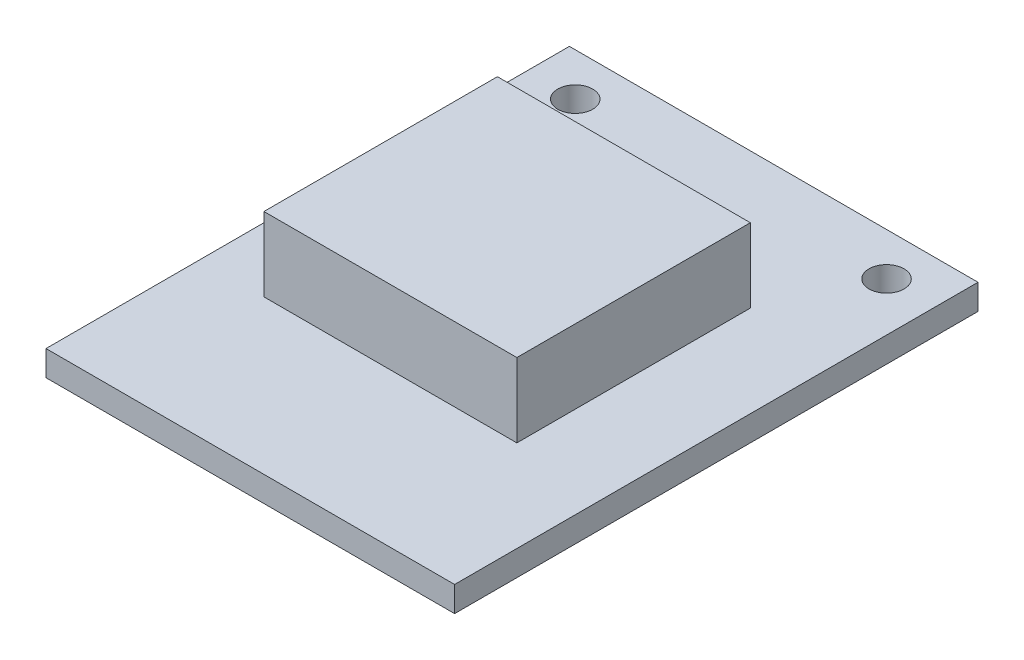
SolidWorks part; units mm, degrees
ref_plane "Front Plane" through (0, 0, 0) normal (0, 0, 1) x (1, 0, 0)
ref_plane "Top Plane" through (0, 0, 0) normal (0, 1, 0) x (1, 0, 0)
ref_plane "Right Plane" through (0, 0, 0) normal (1, 0, 0) x (0, 0, -1)
sketch "Sketch1" plane through (0, 0, 0) normal (0, 1, 0) x (1, 0, 0)
  line L0 (1.143, 0) -> (19.177, 0) construction
  line L1 (10.16, 2.794) -> (10.16, 0) construction
  line L3 (-3.175, 2.794) -> (23.495, 2.794)
  line L4 (-3.175, 2.794) -> (-3.175, -31.369)
  line L5 (-3.175, -31.369) -> (23.495, -31.369)
  line L6 (23.495, 2.794) -> (23.495, -31.369)
  circle A0 centre (0, 0) radius 1.143
  circle A1 centre (20.32, 0) radius 1.143
  point P5 (1.143, 0)
  point P6 (19.177, 0)
  point P7 (-1.143, 0)
  point P14 (21.463, 0)
  point P15 (0, 1.143)
  dimension "D1" = 18.034
  dimension "D2" = 22.606
  dimension "D3" = 26.67
  dimension "D4" = 34.163
  dimension "D5" = 1.651
extrude "Boss-Extrude1" add sketch "Sketch1" along normal blind 1.651
sketch "Sketch2" plane through (0, 1.651, 0) normal (0, 1, 0) x (1, 0, 0)
  line L1 (1.016, -6.096) -> (17.526, -6.096)
  line L2 (1.016, -6.096) -> (1.016, -21.336)
  line L3 (1.016, -21.336) -> (17.526, -21.336)
  line L4 (17.526, -6.096) -> (17.526, -21.336)
  line L8 (-3.175, 2.794) -> (-3.175, -31.369)
  line L9 (-3.175, -31.369) -> (23.495, -31.369)
  line L10 (23.495, -31.369) -> (23.495, 2.794)
  line L11 (23.495, 2.794) -> (-3.175, 2.794)
  line L12 (-3.175, 2.794) -> (-3.175, -31.369)
  line L13 (-3.175, -31.369) -> (23.495, -31.369)
  line L14 (23.495, -31.369) -> (23.495, 2.794)
  line L15 (23.495, 2.794) -> (-3.175, 2.794)
  dimension "D1" = 0
  dimension "D2" = 4.191
  dimension "D3" = 8.89
  dimension "D4" = 5.969
  dimension "D5" = 10.033
extrude "Boss-Extrude2" add sketch "Sketch2" along normal blind 4.826 contours L4 L1 L2 L3
